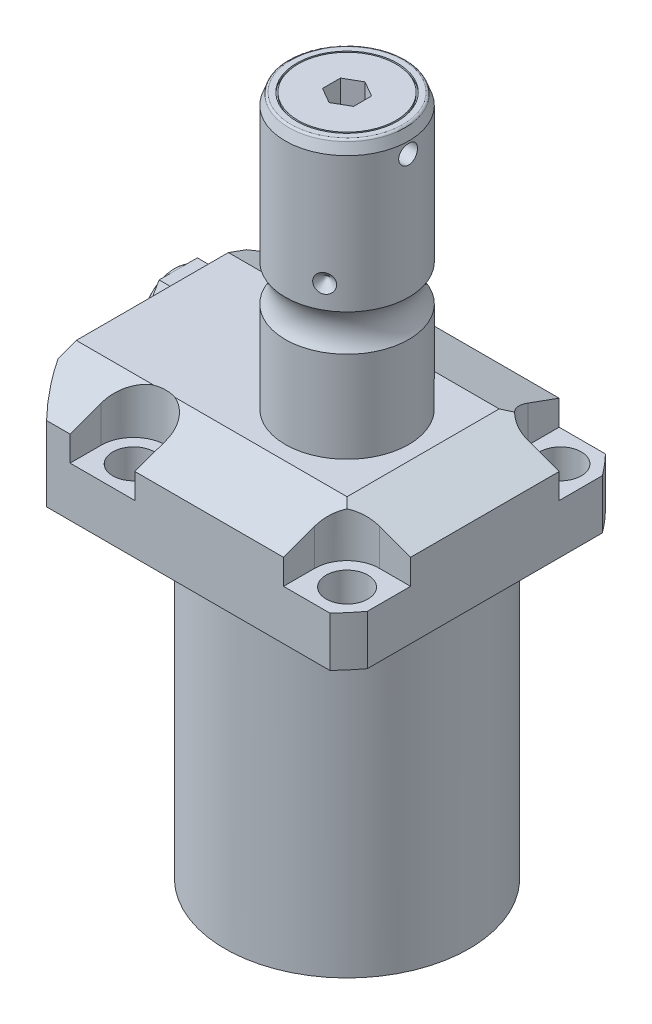
SolidWorks part; units mm, degrees
material "Alloy Steel"
ref_plane "Front Plane" through (0, 0, 0) normal (0, 0, 1) x (1, 0, 0)
ref_plane "Top Plane" through (0, 0, 0) normal (0, 1, 0) x (1, 0, 0)
ref_plane "Right Plane" through (0, 0, 0) normal (1, 0, 0) x (0, 0, -1)
sketch "Sketch1" plane through (0, 0, 0) normal (0, -1, 0) x (0, 0, 1)
  line L0 (-35.433, 50.063) -> (35.433, 50.063)
  line L1 (35.433, 50.063) -> (35.433, -35.433)
  line L2 (35.433, -35.433) -> (-35.433, -35.433)
  line L3 (-35.433, -35.433) -> (-35.433, 50.063)
  line L4 (0, 0) -> (0, -60.6467) construction
  dimension "D1" = 35.433
  dimension "D2" = 85.496
  dimension "D3" = 70.866
extrude "Extrude1" add sketch "Sketch1" against normal blind 104.521
sketch "Sketch2" plane through (0, 0, 0) normal (0, -1, 0) x (1, 0, 0)
  circle A0 centre (-5.4102, 0) radius 50.8
  dimension "D1" = 101.6
  dimension "D2" = 5.4102
extrude "Cut-Extrude1" cut sketch "Sketch2" against normal through all flip side to cut
sketch "Sketch3" plane through (0, 0, 0) normal (1, 0, 0) x (0, 0, -1)
  line L0 (31.3945, 0) -> (31.3945, 79.502)
  line L1 (31.3945, 79.502) -> (76.5937, 79.502)
  line L2 (76.5937, 79.502) -> (76.5937, 0)
  line L3 (76.5937, 0) -> (31.3945, 0)
  line L4 (0, -93.345) -> (0, 4.445) construction
  line L5 (24.2233, 0) -> (-24.2233, 0) construction
  dimension "D1" = 62.789
  dimension "D2" = 153.1874
  dimension "D3" = 79.502
revolve "Cut-Revolve1" cut sketch "Sketch3" angle 360 about L4
fillet "Fillet1" radius 0.381 1 edges at (0, 79.502, -31.3945)
sketch "Sketch4" plane through (0, 104.521, 0) normal (0, 1, 0) x (-1, 0, 0)
  line L0 (-35.433, -30.2072) -> (-35.433, 30.2072) construction
  line L1 (41.8127, 35.433) -> (-30.9923, 35.433) construction
  line L2 (-19.1008, -35.433) -> (-19.1008, -27.432)
  line L3 (-35.433, -35.433) -> (-19.1008, -35.433)
  line L4 (-35.433, -19.1008) -> (-35.433, -35.433)
  line L5 (-27.432, -19.1008) -> (-35.433, -19.1008)
  line L6 (35.7632, -35.433) -> (19.1008, -35.433)
  line L7 (19.1008, 35.433) -> (19.1008, 27.432)
  line L8 (35.7632, 35.433) -> (35.7632, 27.432)
  line L9 (35.7632, 35.433) -> (19.1008, 35.433)
  line L10 (-27.432, 19.1008) -> (-35.433, 19.1008)
  line L11 (-35.433, 19.1008) -> (-35.433, 35.433)
  line L12 (-35.433, 35.433) -> (-19.1008, 35.433)
  line L13 (-19.1008, 35.433) -> (-19.1008, 27.432)
  line L14 (-48.9217, 0) -> (49.4551, 0) construction
  line L15 (35.7632, -35.433) -> (35.7632, -27.432)
  line L16 (19.1008, -35.433) -> (19.1008, -27.432)
  arc A0 (19.1008, -27.432) -> (35.7632, -27.432) centre (27.432, -27.432) cw
  arc A1 (-27.432, -19.1008) -> (-19.1008, -27.432) centre (-27.432, -27.432) cw
  arc A2 (-27.432, 19.1008) -> (-19.1008, 27.432) centre (-27.432, 27.432) ccw
  arc A3 (19.1008, 27.432) -> (35.7632, 27.432) centre (27.432, 27.432) ccw
  dimension "D2" = 8.3312
  dimension "D1" = 27.432
  dimension "D3" = 27.432
  dimension "D4" = 54.864
extrude "Cut-Extrude2" cut sketch "Sketch4" against normal blind 12.243
sketch "Sketch5" plane through (0, 0, 0) normal (1, 0, 0) x (0, 0, -1)
  line L0 (-19.558, 104.521) -> (-35.433, 98.743)
  line L1 (0, 0) -> (0, 154.1081) construction
  line L2 (-19.558, 104.521) -> (-35.433, 104.521)
  line L3 (-35.433, 104.521) -> (-35.433, 98.743)
  dimension "D1" = 15.875
  dimension "D2" = 20
extrude "Cut-Extrude9" cut sketch "Sketch5" against normal through all and the other way through all
mirror "Mirror1" about plane through (0, 0, 0) normal (0, 0, 1) of "Cut-Extrude9"
sketch "Sketch9" plane through (0, 0, 0) normal (0, 0, 1) x (1, 0, 0)
  line L0 (19.558, 104.521) -> (35.433, 98.743)
  line L1 (35.433, 98.743) -> (35.433, 104.521)
  line L2 (35.433, 104.521) -> (19.558, 104.521)
  dimension "D1" = 15.875
  dimension "D2" = 20
extrude "Cut-Extrude7" cut sketch "Sketch9" against normal through all and the other way through all
ref_plane "Plane14" through (-35.0774, 0, 0) normal (1, 0, 0) x (0, 0, -1)
sketch "Sketch20" plane through (-35.0774, 88.9, -18.1102) normal (1, 0, 0) x (0, 1, 0)
  line L0 (-88.9, 18.1102) -> (39.8401, 18.1102) construction
  line L1 (-7.2797, 32.639) -> (36.9042, 32.639) construction
  line L2 (-9.398, 38.3413) -> (-7.9502, 38.3413)
  line L3 (-9.398, -6.1131) -> (-9.398, 42.3335) construction
  line L4 (-7.9502, 38.3413) -> (-7.9502, 35.8902)
  line L5 (-7.9502, 35.8902) -> (-6.9342, 35.8902)
  line L6 (-6.9342, 35.8902) -> (-6.9342, 33.8836)
  line L7 (-6.9342, 33.8836) -> (4.0386, 33.8836)
  line L8 (4.0386, 33.8836) -> (4.0386, 32.639)
  line L9 (4.0386, 32.639) -> (-9.398, 32.639)
  line L10 (-9.398, 38.3413) -> (-9.398, 32.639)
  dimension "D1" = 14.5288
  dimension "D2" = 11.4046
  dimension "D3" = 1.4478
  dimension "D4" = 6.5024
  dimension "D5" = 1.016
  dimension "D6" = 2.4892
  dimension "D7" = 10.9728
revolve "Cut-Revolve4" cut sketch "Sketch20" angle 360 about L1
mirror "Mirror10" about plane through (0, 0, 0) normal (0, 0, 1) of "Cut-Revolve4"
sketch "Sketch10" plane through (-35.0774, 88.9, -18.1102) normal (1, 0, 0) x (0, 1, 0)
  line L0 (-1.0325, 3.5814) -> (1.5659, 3.5814) construction
  line L1 (4.0386, 4.826) -> (-6.9342, 4.826) construction
  line L2 (-6.9342, 2.3368) -> (4.0386, 2.3368) construction
  line L4 (-9.398, -12.097) -> (-9.398, 48.3174) construction
  circle A0 centre (-9.1313, 8.1026) radius 1.1811
  dimension "D1" = 2.3622
  dimension "D2" = 0.2667
  dimension "D3" = 9.0424
revolve "Revolve4" add sketch "Sketch10" angle 360 about L0
mirror "Mirror12" about plane through (0, 0, 0) normal (0, 0, 1) of bodies 135
sketch "Sketch15" plane through (0, 0, 0) normal (1, 0, 0) x (0, 0, -1)
  line L0 (0, 104.521) -> (15.875, 104.521)
  line L1 (15.875, 104.521) -> (15.875, 127.9049)
  line L2 (15.875, 137.3191) -> (15.875, 172.109)
  line L3 (14.8118, 175.03) -> (0, 175.03)
  line L4 (0, 175.03) -> (0, 104.521)
  line L5 (0, 250.2908) -> (0, 28.9095) construction
  line L6 (19.558, 104.521) -> (-19.558, 104.521) construction
  line L7 (14.8118, 175.03) -> (15.875, 172.109)
  line L8 (-31.3945, 0) -> (31.3945, 0) construction
  arc A0 (15.875, 137.3191) -> (15.875, 127.9049) centre (22.2504, 132.612) ccw
  dimension "D2" = 20
  dimension "D4" = 7.9248
  dimension "D6" = 28.6512
  dimension "D1" = 175.03
  dimension "D3" = 31.75
  dimension "D5" = 42.418
  dimension "D7" = 2.921
revolve "Revolve3" add sketch "Sketch15" angle 360 about L5
hole_wizard "Hole1" positions "Sketch18" profile "Sketch17" legacy end condition up to next
sketch "Sketch18" plane through (0, 92.278, 0) normal (0, 1, 0) x (-1, 0, 0)
  arc A0 (35.7632, -27.432) -> (19.1008, -27.432) centre (27.432, -27.432) ccw construction
  arc A1 (19.1008, 27.432) -> (35.7632, 27.432) centre (27.432, 27.432) ccw construction
  arc A2 (-27.432, 19.1008) -> (-19.1008, 27.432) centre (-27.432, 27.432) ccw construction
  arc A3 (-19.1008, -27.432) -> (-27.432, -19.1008) centre (-27.432, -27.432) ccw construction
  point P0 (-27.432, -27.432)
  point P1 (-27.432, 27.432)
  point P3 (27.432, 27.432)
  point P5 (27.432, -27.432)
sketch "Sketch17" plane through (27.432, 92.278, -27.432) normal (1, 0, 0) x (0, 0, 1)
  line L0 (0, 0) -> (0, 12.776)
  line L1 (0, 12.776) -> (5.3594, 12.776)
  line L2 (5.3594, 12.776) -> (5.3594, 0)
  line L3 (5.3594, 0) -> (0, 0)
  line L4 (0, 110) -> (0, -10) construction
  dimension "Diameter" = 10.7188
  dimension "Depth" = 12.776
chamfer "Chamfer1" distance 0.635 angle 45 2 edges at (-35.0774, 81.9658, 13.2842) (-35.0774, 81.9658, -13.2842)
ref_plane "Plane15" through (0, 92.5068, 0) normal (0, -1, 0) x (1, 0, 0)
sketch "Sketch21" plane through (0, 92.5068, 0) normal (0, -1, 0) x (1, 0, 0)
  line L0 (-57.5495, -12.9794) -> (-2.9353, -12.9794) construction
  line L1 (-50.063, -1.9304) -> (-49.809, -1.9304)
  line L2 (-49.809, -1.9304) -> (-49.809, -6.3246)
  line L3 (-49.809, -6.3246) -> (-49.0978, -7.0358)
  line L4 (-49.0978, -7.0358) -> (-35.6358, -7.0358)
  line L5 (-35.6358, -7.0358) -> (-35.6358, -12.9794)
  line L6 (-35.6358, -12.9794) -> (-50.063, -12.9794)
  line L7 (-50.063, 24.2233) -> (-50.063, -24.2233) construction
  line L8 (-50.063, -12.9794) -> (-50.063, -1.9304)
  dimension "D1" = 12.9794
  dimension "D2" = 0.254
  dimension "D3" = 22.098
  dimension "D4" = 45
  dimension "D5" = 0.7112
  dimension "D6" = 11.8872
  dimension "D7" = 14.1732
revolve "Cut-Revolve5" cut sketch "Sketch21" angle 360 about L0
mirror "Mirror13" about plane through (0, 0, 0) normal (0, 0, 1) of "Cut-Revolve5"
sketch "Sketch22" plane through (-49.809, 0, 0) normal (-1, 0, 0) x (0, 0, 1)
  line L1 (-3.1541, 92.5068) -> (-8.0667, 101.0158)
  line L2 (-8.0667, 101.0158) -> (-17.8921, 101.0158)
  line L3 (-17.8921, 101.0158) -> (-22.8047, 92.5068)
  line L4 (-22.8047, 92.5068) -> (-17.8921, 83.9978)
  line L5 (-17.8921, 83.9978) -> (-8.0667, 83.9978)
  line L6 (-8.0667, 83.9978) -> (-3.1541, 92.5068)
  circle A0 centre (-12.9794, 92.5068) radius 8.509 construction
  dimension "D1" = 17.018
extrude "Extrude2" add sketch "Sketch22" along normal blind 7.874
sketch "Sketch23" plane through (0, 92.5068, 0) normal (0, -1, 0) x (1, 0, 0)
  line L0 (-77.4666, -12.9794) -> (-13.4137, -12.9794) construction
  line L1 (-57.683, -2.8194) -> (-56.383, -2.8194)
  line L3 (-56.383, -2.8194) -> (-56.383, -4.4704)
  line L4 (-56.383, -4.4704) -> (-56.413, -4.4704)
  line L5 (-57.683, -8.0667) -> (-57.683, -3.1541) construction
  line L6 (-35.6358, -12.9794) -> (-49.0978, -12.9794) construction
  line L7 (-57.683, -2.8194) -> (-57.683, -5.7404)
  line L8 (-49.809, -1.9304) -> (-49.809, -24.0284) construction
  line L10 (-49.809, -2.8194) -> (-50.809, -2.8194)
  line L11 (-49.809, -2.8194) -> (-49.809, -4.4704)
  line L12 (-49.809, -4.4704) -> (-50.809, -4.4704)
  line L13 (-50.809, -2.8194) -> (-50.809, -4.4704)
  arc A0 (-56.413, -4.4704) -> (-57.683, -5.7404) centre (-56.413, -5.7404) ccw
  dimension "D1" = 1.27
  dimension "D2" = 1.3
  dimension "D3" = 17.018
  dimension "D4" = 1
  dimension "D5" = 20.32
revolve "Cut-Revolve6" cut sketch "Sketch23" angle 360 about L0
fillet "Fillet2" radius 0.635 1 edges at (0, 175.03, 14.8118)
sketch "Sketch24" plane through (0, 175.03, 0) normal (0, 1, 0) x (1, 0, 0)
  circle A0 centre (0, 0) radius 12.954
  circle A1 centre (0, 0) radius 12.573
  dimension "D1" = 25.908
  dimension "D2" = 25.146
extrude "Cut-Extrude10" cut sketch "Sketch24" against normal blind 0.5
sketch "Sketch25" plane through (0, 175.03, 0) normal (0, 1, 0) x (1, 0, 0)
  line L1 (4, -2.3094) -> (4, 2.3094)
  line L2 (4, 2.3094) -> (0, 4.6188)
  line L3 (0, 4.6188) -> (-4, 2.3094)
  line L4 (-4, 2.3094) -> (-4, -2.3094)
  line L5 (-4, -2.3094) -> (0, -4.6188)
  line L6 (0, -4.6188) -> (4, -2.3094)
  circle A0 centre (0, 0) radius 4 construction
  dimension "D1" = 8
extrude "Cut-Extrude11" cut sketch "Sketch25" against normal blind 8
sketch "Sketch26" plane through (0, 0, 0) normal (0, 0, 1) x (1, 0, 0)
  line L0 (-39.772, 143.3) -> (35.3173, 143.3) construction
  line L1 (-15.875, 145.713) -> (-13.462, 143.3)
  line L2 (-15.875, 172.109) -> (-15.875, 137.3191) construction
  line L3 (-13.462, 143.3) -> (-15.875, 143.3)
  line L4 (-15.875, 143.3) -> (-15.875, 145.713)
  arc A0 (-15.875, 127.9049) -> (-15.875, 137.3191) centre (-22.2504, 132.612) ccw construction
  dimension "D1" = 45
  dimension "D2" = 4.826
  dimension "D3" = 10.688
revolve "Cut-Revolve7" cut sketch "Sketch26" angle 360 about L0
pattern_circular "CirPattern1" count 3 over 360 about axis through (0, 250.2908, 0) along (0, 1, 0) of "Cut-Revolve7"
sketch "Sketch27" plane through (0, 0, 0) normal (0, 0, 1) x (1, 0, 0)
  line L0 (5.3741, 169.188) -> (21.6654, 169.188) construction
  line L1 (15.875, 137.3191) -> (15.875, 172.109) construction
  line L2 (15.875, 171.601) -> (12.065, 171.601)
  line L3 (15.875, 171.601) -> (15.875, 169.188)
  line L4 (15.875, 169.188) -> (12.065, 169.188)
  line L5 (12.065, 171.601) -> (12.065, 169.188)
  line L6 (12.573, 175.03) -> (-12.573, 175.03) construction
  dimension "D1" = 4.826
  dimension "D2" = 3.81
  dimension "D3" = 5.842
revolve "Cut-Revolve8" cut sketch "Sketch27" angle 360 about L0
